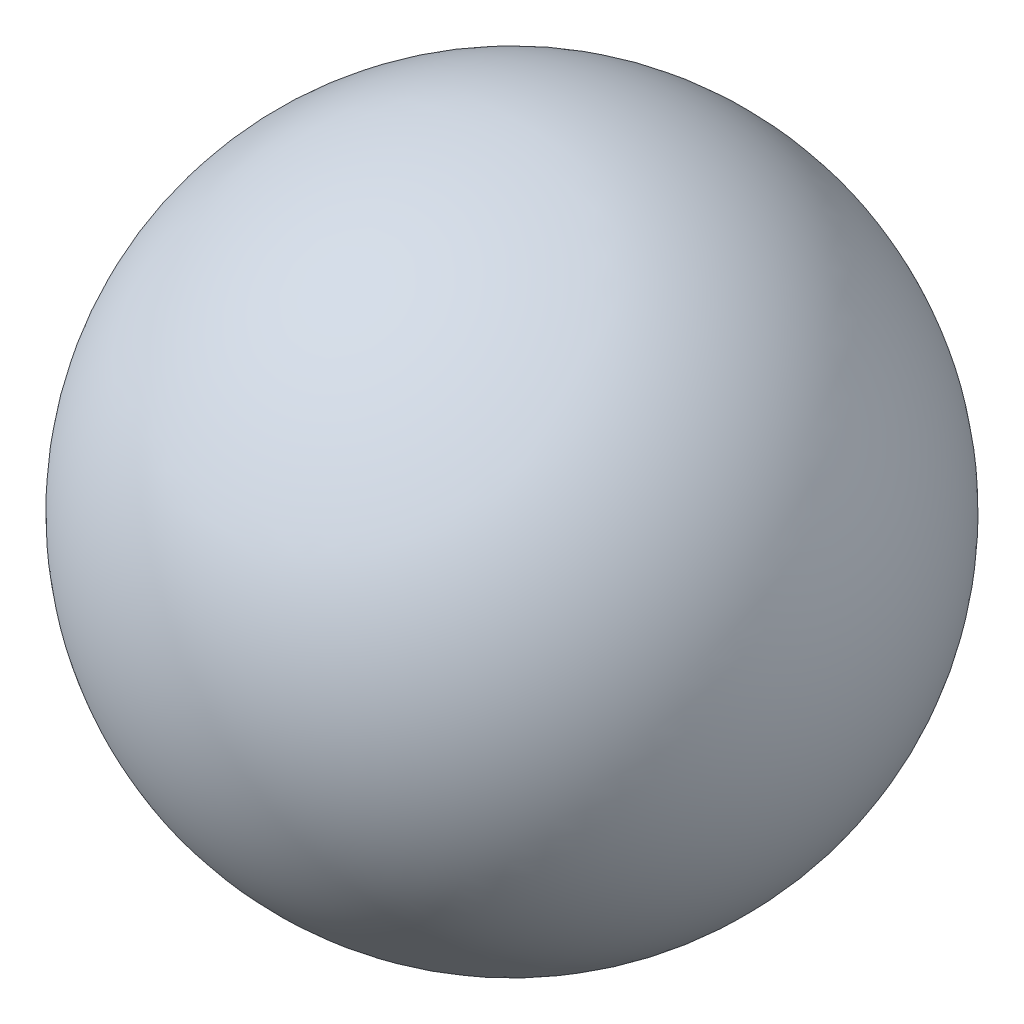
SolidWorks part; units mm, degrees
ref_plane "Front Plane" through (0, 0, 0) normal (0, 0, 1) x (1, 0, 0)
ref_plane "Top Plane" through (0, 0, 0) normal (0, 1, 0) x (1, 0, 0)
ref_plane "Right Plane" through (0, 0, 0) normal (1, 0, 0) x (0, 0, -1)
sketch "Sketch1" plane through (0, 0, 0) normal (0, 1, 0) x (1, 0, 0)
  line L0 (0, 30) -> (0, -30)
  arc A0 (0, 30) -> (0, -30) centre (0, 0) ccw
  dimension "D1" = 60
revolve "Revolve1" add sketch "Sketch1" angle 360 about L0
